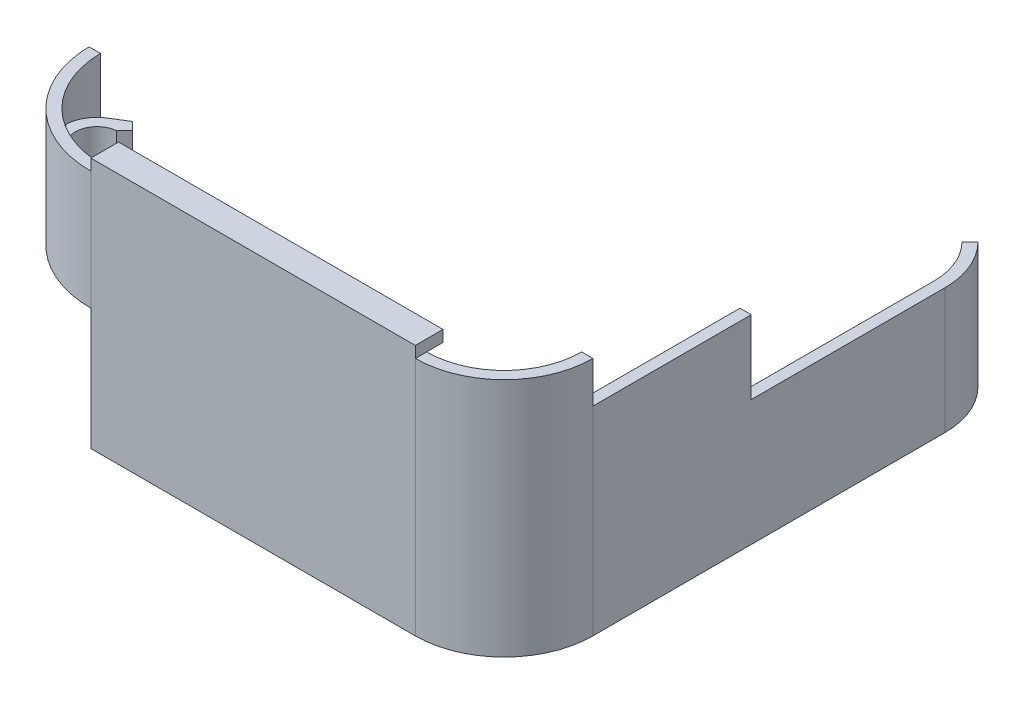
SolidWorks part; units mm, degrees
ref_plane "Front Plane" through (0, 0, 0) normal (0, 0, 1) x (1, 0, 0)
ref_plane "Top Plane" through (0, 0, 0) normal (0, 1, 0) x (1, 0, 0)
ref_plane "Right Plane" through (0, 0, 0) normal (1, 0, 0) x (0, 0, -1)
sketch "Sketch8" plane through (0, 0, 0) normal (0, 1, 0) x (1, 0, 0)
  line L0 (0, -21.844) -> (72.898, -21.844)
  arc A1 (72.898, -21.844) -> (90.3097, -4.4323) centre (72.898, -4.4323) ccw
  arc A3 (0, -21.844) -> (-21.8407, -0.3812) centre (0, 0) cw
  dimension "D1" = 72.898
  dimension "D3" = 21.844
  dimension "D5" = 17.4117
extrude "Extrude-Thin1" add sketch "Sketch8" along normal blind 53.975 thin
sketch "Sketch9" plane through (0, 0, 0) normal (0, 1, 0) x (1, 0, 0)
  line L0 (0, 0) -> (-11.4983, -11.4983) construction
  circle A0 centre (-11.4983, -11.4983) radius 4.6228 construction
  arc A1 (-21.8407, -0.3812) -> (0, -21.844) centre (0, 0) ccw construction
  dimension "D1" = 16.2611
  dimension "D2" = 9.2456
sketch "Sketch10" plane through (0, 0, 0) normal (0, 1, 0) x (1, 0, 0)
  line L4 (0, 0) -> (-20.7337, -20.7337) construction
  line L15 (-6.6412, -11.9364) -> (-4.8435, -10.1387)
  line L16 (-4.8435, -10.1387) -> (-3.0459, -11.9364)
  line L17 (-3.0459, -11.9364) -> (-5.3839, -15.6962)
  line L21 (-11.9364, -3.0459) -> (-15.6962, -5.3839)
  line L22 (-10.1387, -4.8435) -> (-11.9364, -3.0459)
  line L23 (-11.9364, -6.6412) -> (-10.1387, -4.8435)
  arc A2 (-10.9599, -18.8955) -> (-18.8955, -10.9599) centre (0, 0) cw
  circle A3 centre (-11.4983, -11.4983) radius 4.6228 construction
  arc A4 (-11.9364, -6.6412) -> (-6.6412, -11.9364) centre (-11.4983, -11.4983) ccw
  arc A6 (-10.9599, -18.8955) -> (-5.3839, -15.6962) centre (-11.4983, -11.4983) ccw
  arc A7 (-18.8955, -10.9599) -> (-15.6962, -5.3839) centre (-11.4983, -11.4983) cw
  dimension "D1" = 0.254
extrude "Boss-Extrude1" add sketch "Sketch10" along normal blind 19.05 from offset 27.94
sketch "Sketch11" plane through (0, 0, 0) normal (0, 1, 0) x (1, 0, 0)
  line L0 (0, -21.844) -> (72.898, -21.844) construction
  line L1 (90.3097, -4.4323) -> (92.8497, -4.4323)
  line L2 (90.3097, -4.4323) -> (90.3097, 74.676)
  line L4 (92.8497, -4.4323) -> (92.8497, 74.676)
  line L5 (85.8267, 85.499) -> (87.6227, 87.2951)
  arc A0 (90.3097, 74.676) -> (85.8267, 85.499) centre (75.0037, 74.676) ccw
  arc A1 (92.8497, 74.676) -> (87.6227, 87.2951) centre (75.0037, 74.676) ccw
  dimension "D4" = 15.306
  dimension "D2" = 17.4117
  dimension "D5" = 2.54
extrude "Boss-Extrude2" add sketch "Sketch11" along normal blind 28.194
sketch "Sketch12" plane through (0, 0, 0) normal (-0.0175, 0, -0.9998) x (-0.9998, 0, 0.0175)
  line L0 (0.3812, 53.975) -> (0.3812, 0) construction
  line L1 (0.3812, 27.305) -> (35.2486, 27.305)
  line L2 (0.3812, 27.305) -> (0.3812, -3.4685)
  line L3 (0.3812, -3.4685) -> (35.2486, -3.4685)
  line L4 (35.2486, 27.305) -> (35.2486, -3.4685)
  line L5 (0.3812, 53.975) -> (-72.5057, 53.975) construction
  dimension "D1" = 26.67
extrude "Cut-Extrude1" cut sketch "Sketch12" against normal through all
sketch "Sketch13" plane through (0, 28.194, 0) normal (0, 1, 0) x (1, 0, 0)
  line L0 (92.8497, -4.4323) -> (92.8497, 74.676) construction
  line L1 (90.3097, -4.4323) -> (92.8497, -4.4323)
  line L2 (90.3097, -4.4323) -> (90.3097, 31.1277)
  line L3 (90.3097, 31.1277) -> (92.8497, 31.1277)
  line L4 (92.8497, -4.4323) -> (92.8497, 31.1277)
  dimension "D1" = 35.56
extrude "Boss-Extrude3" add sketch "Sketch13" along normal blind 16.51
sketch "Sketch14" plane through (0, 53.975, 0) normal (0, 1, 0) x (1, 0, 0)
  line L1 (0, -24.384) -> (72.898, -24.384)
  line L2 (0, -24.384) -> (0, -18.1608)
  line L3 (0, -18.1608) -> (72.898, -18.1608)
  line L4 (72.898, -24.384) -> (72.898, -18.1608)
extrude "Boss-Extrude4" add sketch "Sketch14" along normal blind 2.54
equation "\"1.8inin\"=2"
